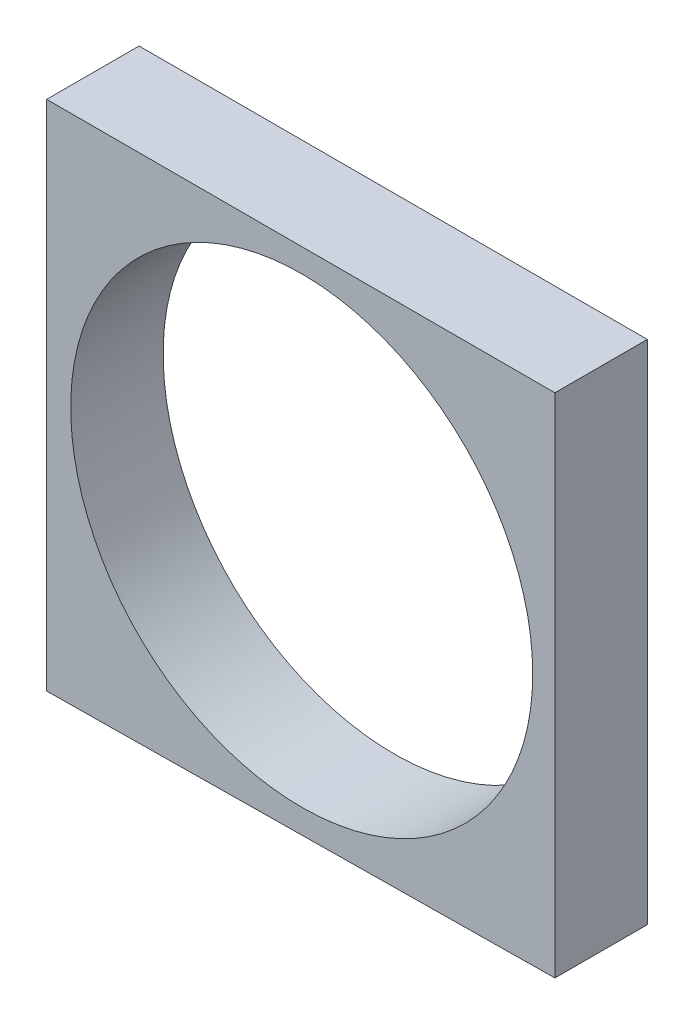
SolidWorks part; units mm, degrees
material "Custom Plastic"
ref_plane "Front Plane" through (0, 0, 0) normal (0, 0, 1) x (1, 0, 0)
ref_plane "Top Plane" through (0, 0, 0) normal (0, 1, 0) x (1, 0, 0)
ref_plane "Right Plane" through (0, 0, 0) normal (1, 0, 0) x (0, 0, -1)
sketch "Sketch1" plane through (0, 0, 0) normal (0, 0, 1) x (1, 0, 0)
  line L3 (-35.052, 34.9885) -> (34.798, 34.9885)
  line L5 (-35.052, 34.9885) -> (-35.052, -35.443)
  line L7 (-35.052, -35.443) -> (34.798, -34.6682)
  line L8 (34.798, -34.6682) -> (34.798, 34.9885)
  circle A0 centre (0, 0) radius 31.75
  dimension "D1" = 34.9885
  dimension "D2" = 63.5
  dimension "D3" = 35.052
  dimension "D4" = 69.85
  dimension "D5" = 35.052
extrude "Boss-Extrude1" add sketch "Sketch1" along normal blind 12.7
